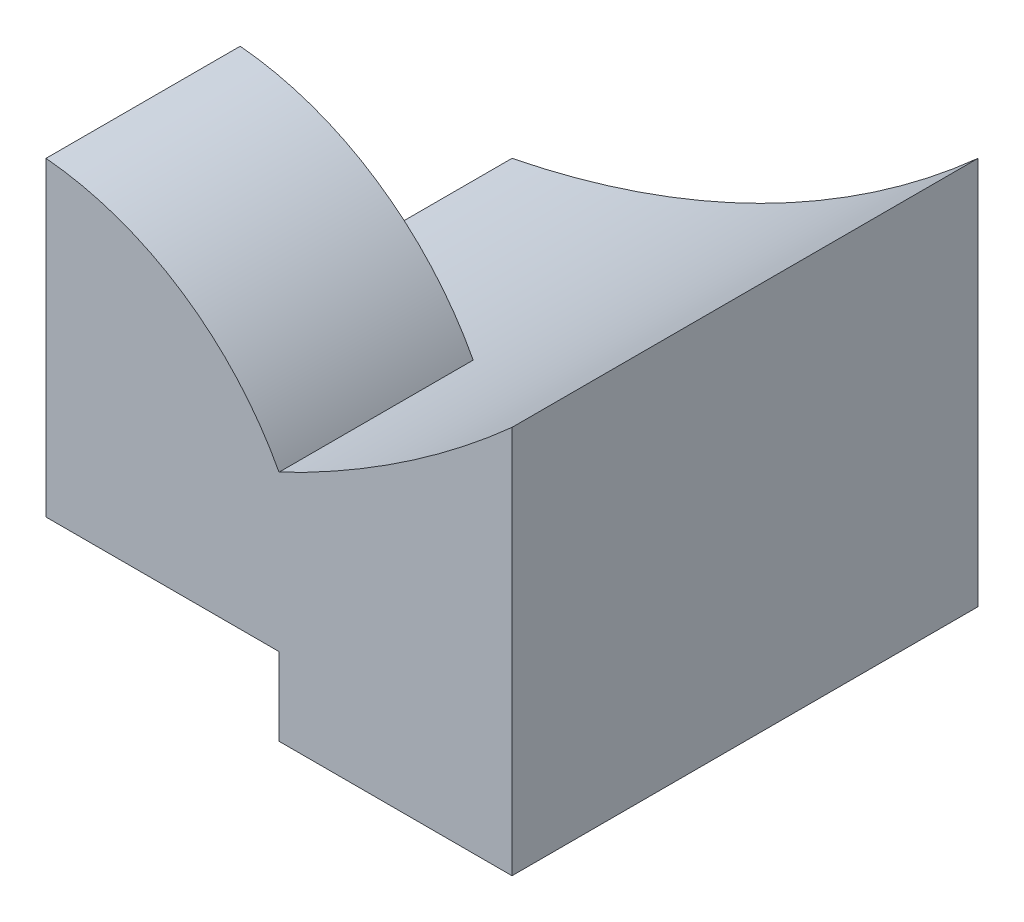
SolidWorks part; units mm, degrees
ref_plane "Front" through (0, 0, 0) normal (0, 0, 1) x (1, 0, 0)
ref_plane "Top" through (0, 0, 0) normal (0, 1, 0) x (1, 0, 0)
ref_plane "Right" through (0, 0, 0) normal (1, 0, 0) x (0, 0, -1)
sketch "Sketch1" plane through (0, 0, 0) normal (0, 1, 0) x (1, 0, 0)
  line L1 (-3, -3) -> (3, -3)
  line L2 (-3, -3) -> (-3, 3)
  line L3 (-3, 3) -> (3, 3)
  line L4 (3, -3) -> (3, 3)
  line L5 (-3, -3) -> (3, 3) construction
  line L6 (-3, 3) -> (3, -3) construction
  point P0 (0, 0)
  dimension "D1" = 6
  dimension "D2" = 6
extrude "Boss-Extrude1" add sketch "Sketch1" along normal blind 5
sketch "Sketch8" plane through (0, 0, 3) normal (0, 0, 1) x (1, 0, 0)
  line L0 (-3, 5) -> (-3, 0) construction
  line L1 (-3, 5) -> (3, 5) construction
  arc A0 (3, 5) -> (-3, 2) centre (-5.5, 14.5) cw
  arc A1 (0, 3) -> (-3, 5) centre (-3.3367, 1.245) ccw
  line M3 (3, 5) -> (-3, 5)
  dimension "D1" = 2
  dimension "D2" = 2
  dimension "D3" = 3
extrude "Cut-Extrude7" cut sketch "Sketch8" against normal blind 12.5 contours A1 A0 M3
sketch "Sketch9" plane through (0, 0, -3) normal (0, 0, -1) x (-1, 0, 0)
  line L0 (3, 5) -> (3, 0) construction
  line L4 (3, 0) -> (3, 5)
  line L5 (-3, 0) -> (3, 0)
  line L6 (-3, 5) -> (-3, 0)
  line L7 (3, 0) -> (3, 5)
  line L8 (-3, 0) -> (3, 0)
  line L9 (-3, 5) -> (-3, 0)
  arc A0 (-3, 5) -> (3, 2) centre (5.5, 14.5) ccw
  arc A3 (3, 5) -> (0, 3) centre (3.3367, 1.245) ccw
  arc A4 (-3, 5) -> (0, 3) centre (5.5, 14.5) ccw
  arc A5 (3, 5) -> (0, 3) centre (3.3367, 1.245) ccw
  arc A6 (-3, 5) -> (0, 3) centre (5.5, 14.5) ccw
  arc M6 (3, 5) -> (0, 3) centre (3.3367, 1.245) ccw
  dimension "D1" = 2
  dimension "D2" = 0
extrude "Cut-Extrude8" cut sketch "Sketch9" against normal blind 3.5 contours A0 L7 M6
sketch "Sketch10" plane through (0, 0, 3) normal (0, 0, 1) x (1, 0, 0)
  line L1 (-3, 0) -> (0, 0)
  line L2 (-3, 0) -> (-3, 1)
  line L3 (-3, 1) -> (0, 1)
  line L4 (0, 0) -> (0, 1)
  dimension "D1" = 1
extrude "Cut-Extrude9" cut sketch "Sketch10" against normal blind 2.5
